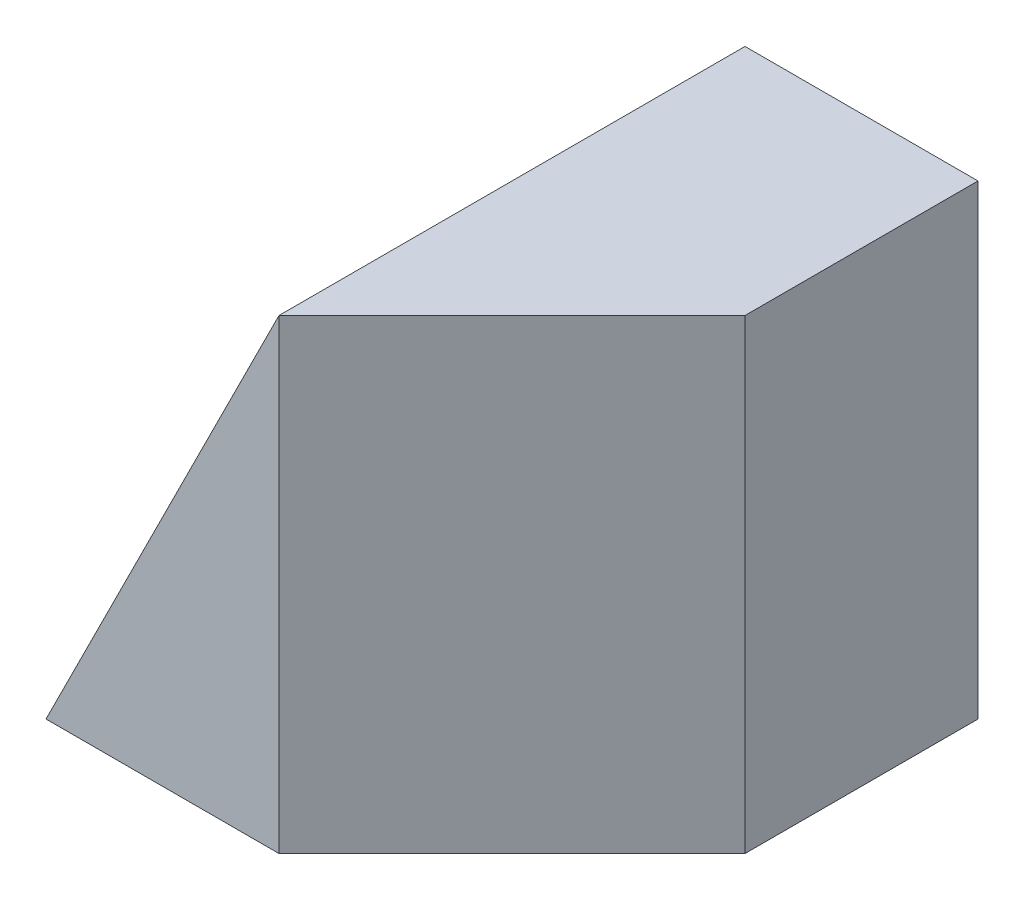
SolidWorks part; units mm, degrees
ref_plane "Front Plane" through (0, 0, 0) normal (0, 0, 1) x (1, 0, 0)
ref_plane "Top Plane" through (0, 0, 0) normal (0, 1, 0) x (1, 0, 0)
ref_plane "Right Plane" through (0, 0, 0) normal (1, 0, 0) x (0, 0, -1)
sketch "Sketch1" plane through (0, 0, 0) normal (0, 0, 1) x (1, 0, 0)
  line L1 (0, 0) -> (40, 0)
  line L2 (0, 0) -> (0, 40)
  line L3 (0, 40) -> (40, 40)
  line L4 (40, 0) -> (40, 40)
  dimension "D1" = 40
  dimension "D2" = 40
extrude "Boss-Extrude1" add sketch "Sketch1" along normal blind 40
sketch "Sketch2" plane through (0, 0, 40) normal (0, 0, 1) x (1, 0, 0)
  line L0 (0, 0) -> (20, 40)
  line L1 (40, 40) -> (0, 40) construction
  line L2 (20, 40) -> (0, 40)
  line L3 (0, 40) -> (0, 0)
extrude "Cut-Extrude1" cut sketch "Sketch2" against normal blind 40
sketch "Sketch3" plane through (0, 40, 0) normal (0, 1, 0) x (1, 0, 0)
  line L0 (20, -40) -> (40, -20)
  line L1 (40, -40) -> (40, 0) construction
  line L2 (40, -20) -> (40, -40)
  line L3 (40, -40) -> (20, -40)
extrude "Cut-Extrude2" cut sketch "Sketch3" against normal blind 40
